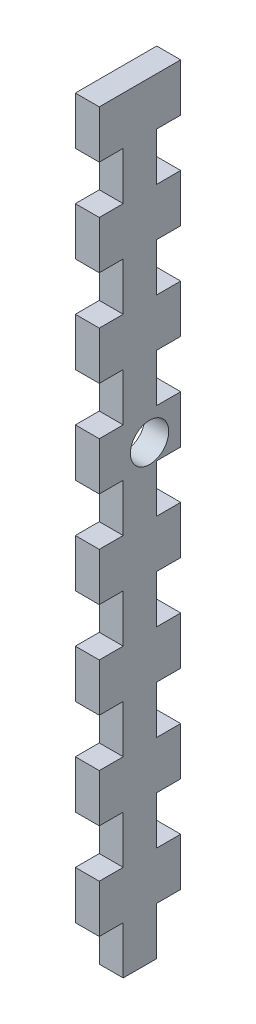
SolidWorks part; units mm, degrees
material "Balsa"
ref_plane "Alzado" through (0, 0, 0) normal (0, 0, 1) x (1, 0, 0)
ref_plane "Planta" through (0, 0, 0) normal (0, 1, 0) x (1, 0, 0)
ref_plane "Vista lateral" through (0, 0, 0) normal (1, 0, 0) x (0, 0, -1)
sketch "Croquis1" plane through (0, 0, 0) normal (1, 0, 0) x (0, 0, -1)
  line L0 (-17.1505, 62.7891) -> (-17.1505, 52.7891)
  line L1 (-17.1505, 92.7891) -> (-0.1505, 92.7891)
  line L2 (-17.1505, 92.7891) -> (-17.1505, -67.2109)
  line L3 (-17.1505, -67.2109) -> (-0.1505, -67.2109)
  line L4 (-0.1505, 92.7891) -> (-0.1505, -67.2109)
  line L5 (-17.1505, 82.7891) -> (-12.1505, 82.7891)
  line L6 (-17.1505, 82.7891) -> (-17.1505, 72.7891)
  line L7 (-17.1505, 72.7891) -> (-12.1505, 72.7891)
  line L8 (-12.1505, 82.7891) -> (-12.1505, 72.7891)
  line L9 (-17.1505, 62.7891) -> (-12.1505, 62.7891)
  line L10 (-12.1505, 62.7891) -> (-12.1505, 52.7891)
  line L11 (-17.1505, 52.7891) -> (-12.1505, 52.7891)
  line L12 (-17.1505, 42.7891) -> (-17.1505, 32.7891)
  line L13 (-17.1505, 42.7891) -> (-12.1505, 42.7891)
  line L14 (-12.1505, 42.7891) -> (-12.1505, 32.7891)
  line L15 (-17.1505, 32.7891) -> (-12.1505, 32.7891)
  line L16 (-17.1505, 22.7891) -> (-17.1505, 12.7891)
  line L17 (-17.1505, 22.7891) -> (-12.1505, 22.7891)
  line L18 (-12.1505, 22.7891) -> (-12.1505, 12.7891)
  line L19 (-17.1505, 12.7891) -> (-12.1505, 12.7891)
  line L20 (-17.1505, 2.7891) -> (-17.1505, -7.2109)
  line L21 (-17.1505, 2.7891) -> (-12.1505, 2.7891)
  line L22 (-12.1505, 2.7891) -> (-12.1505, -7.2109)
  line L23 (-17.1505, -7.2109) -> (-12.1505, -7.2109)
  line L24 (-17.1505, -17.2109) -> (-17.1505, -27.2109)
  line L25 (-17.1505, -17.2109) -> (-12.1505, -17.2109)
  line L26 (-12.1505, -17.2109) -> (-12.1505, -27.2109)
  line L27 (-17.1505, -27.2109) -> (-12.1505, -27.2109)
  line L28 (-17.1505, -37.2109) -> (-17.1505, -47.2109)
  line L29 (-17.1505, -37.2109) -> (-12.1505, -37.2109)
  line L30 (-12.1505, -37.2109) -> (-12.1505, -47.2109)
  line L31 (-17.1505, -47.2109) -> (-12.1505, -47.2109)
  line L32 (-17.1505, -57.2109) -> (-17.1505, -67.2109)
  line L33 (-17.1505, -57.2109) -> (-12.1505, -57.2109)
  line L34 (-12.1505, -57.2109) -> (-12.1505, -67.2109)
  line L35 (-17.1505, -67.2109) -> (-12.1505, -67.2109)
  line L37 (-0.1505, 72.7891) -> (-5.1505, 72.7891)
  line L38 (-5.1505, 82.7891) -> (-5.1505, 72.7891)
  line L39 (-0.1505, 82.7891) -> (-5.1505, 82.7891)
  line L40 (-0.1505, 82.7891) -> (-0.1505, 72.7891)
  line L41 (-0.1505, 62.7891) -> (-5.1505, 62.7891)
  line L42 (-5.1505, 62.7891) -> (-5.1505, 52.7891)
  line L43 (-0.1505, 52.7891) -> (-5.1505, 52.7891)
  line L44 (-0.1505, 62.7891) -> (-0.1505, 52.7891)
  line L45 (-0.1505, 42.7891) -> (-5.1505, 42.7891)
  line L46 (-5.1505, 42.7891) -> (-5.1505, 32.7891)
  line L47 (-0.1505, 32.7891) -> (-5.1505, 32.7891)
  line L48 (-0.1505, 42.7891) -> (-0.1505, 32.7891)
  line L49 (-0.1505, 22.7891) -> (-5.1505, 22.7891)
  line L50 (-5.1505, 22.7891) -> (-5.1505, 12.7891)
  line L51 (-0.1505, 12.7891) -> (-5.1505, 12.7891)
  line L52 (-0.1505, 22.7891) -> (-0.1505, 12.7891)
  line L53 (-0.1505, 2.7891) -> (-5.1505, 2.7891)
  line L54 (-5.1505, 2.7891) -> (-5.1505, -7.2109)
  line L55 (-0.1505, -7.2109) -> (-5.1505, -7.2109)
  line L56 (-0.1505, 2.7891) -> (-0.1505, -7.2109)
  line L57 (-0.1505, -17.2109) -> (-5.1505, -17.2109)
  line L58 (-5.1505, -17.2109) -> (-5.1505, -27.2109)
  line L59 (-0.1505, -27.2109) -> (-5.1505, -27.2109)
  line L60 (-0.1505, -17.2109) -> (-0.1505, -27.2109)
  line L61 (-0.1505, -37.2109) -> (-5.1505, -37.2109)
  line L62 (-5.1505, -37.2109) -> (-5.1505, -47.2109)
  line L63 (-0.1505, -47.2109) -> (-5.1505, -47.2109)
  line L64 (-0.1505, -37.2109) -> (-0.1505, -47.2109)
  line L65 (-0.1505, -57.2109) -> (-5.1505, -57.2109)
  line L66 (-5.1505, -57.2109) -> (-5.1505, -67.2109)
  line L67 (-0.1505, -67.2109) -> (-5.1505, -67.2109)
  line L68 (-0.1505, -57.2109) -> (-0.1505, -67.2109)
  dimension "D1" = 160
  dimension "D2" = 17
  dimension "D3" = 10
  dimension "D4" = 10
  dimension "D5" = 5
  dimension "D6" = 8
extrude "Saliente-Extruir1" add sketch "Croquis1" along normal blind 5 contours L66 L65 L4 L63 L62 L61 L59 L58 L57 L55 L54 L53 L51 L50 L49 L47 L46 L45 L43 L42 L41 L37 L38 L39 L1 L2 L5 L8 L7 L9 L10 L11 L13 L14 L15 L17 L18 L19 L21 L22
sketch "Croquis2" plane through (5, 0, 0) normal (1, 0, 0) x (0, 0, -1)
  line L0 (-18.733, 26.8741) -> (2.4599, 26.8741) construction
  line L1 (-17.1505, 32.7891) -> (-17.1505, 22.7891) construction
  line L2 (-0.1505, 32.7891) -> (-0.1505, 22.7891) construction
  line L3 (-6.6505, 92.7891) -> (-6.6505, -67.2109) construction
  line L4 (-17.1505, 22.7891) -> (-12.1505, 22.7891) construction
  line L8 (-12.1505, 82.7891) -> (-12.1505, 72.7891) construction
  line L9 (-17.1505, 30.2891) -> (-0.1505, 30.2891) construction
  line L10 (-17.1505, 32.7891) -> (-12.1505, 32.7891) construction
  line L13 (-17.1505, 23.4591) -> (-0.1505, 23.4591) construction
  circle A0 centre (-6.6505, 26.8741) radius 4
  point P20 (0, 0)
  dimension "D1" = 8
  dimension "D2" = 3.415
  dimension "D3" = 5.5
  dimension "D4" = 2.5
  dimension "D6" = 0.67
extrude "Cortar-Extruir1" cut sketch "Croquis2" against normal blind 5
